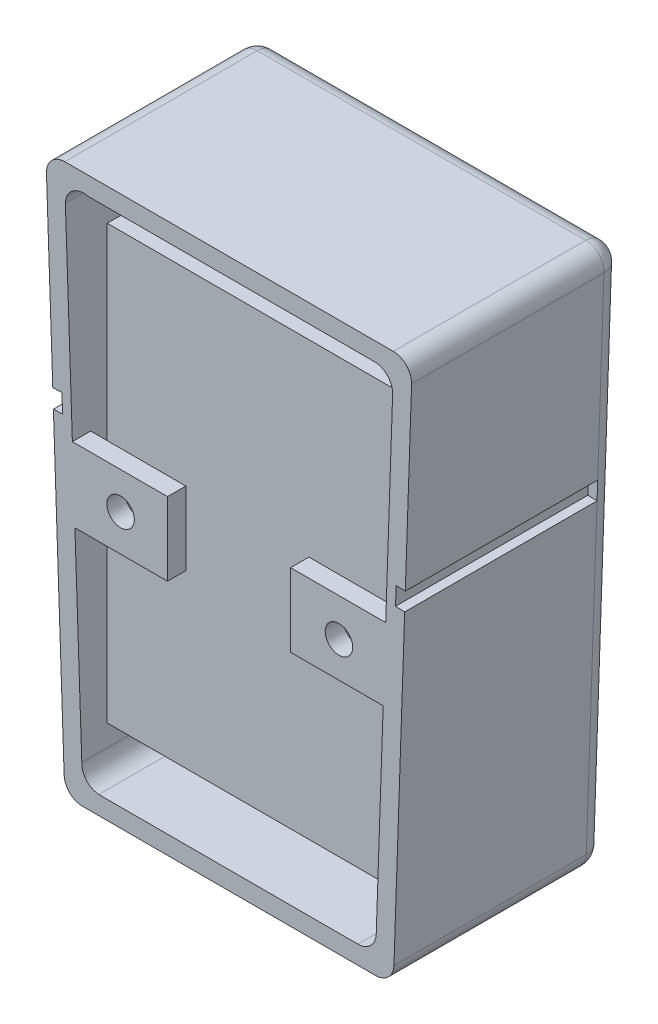
SolidWorks part; units mm, degrees
ref_plane "Front Plane" through (0, 0, 0) normal (0, 0, 1) x (1, 0, 0)
ref_plane "Top Plane" through (0, 0, 0) normal (0, 1, 0) x (1, 0, 0)
ref_plane "Right Plane" through (0, 0, 0) normal (1, 0, 0) x (0, 0, -1)
sketch "Sketch1" plane through (0, 0, 0) normal (0, 0, 1) x (1, 0, 0)
  line L8 (-22.7709, 76.1547) -> (22.7709, 76.1547)
  line L9 (25.3094, 73.5272) -> (22.8585, 2.4525)
  line L10 (20.32, 0) -> (-20.32, 0)
  line L11 (0, 76.1547) -> (0, 0) construction
  line L12 (-25.3094, 73.5272) -> (-22.8585, 2.4525)
  line L13 (-19.5413, 73.6147) -> (20.1418, 73.6147)
  line L14 (22.6803, 70.9872) -> (20.4046, 4.9925)
  line L15 (17.8661, 2.54) -> (-18.0612, 2.54)
  line L16 (-22.688, 71.2103) -> (-20.4122, 5.2126)
  arc A0 (22.8585, 2.4525) -> (20.32, 0) centre (20.32, 2.54) cw
  arc A1 (22.7709, 76.1547) -> (25.3094, 73.5272) centre (22.7709, 73.6147) cw
  arc A2 (-22.8585, 2.4525) -> (-20.32, 0) centre (-20.32, 2.54) ccw
  arc A3 (-22.7709, 76.1547) -> (-25.3094, 73.5272) centre (-22.7709, 73.6147) ccw
  circle A4 centre (0, 58.5396) radius 3.75
  circle A5 centre (0, 21.6223) radius 12.75
  arc A6 (20.4046, 4.9925) -> (17.8661, 2.54) centre (17.8661, 5.08) cw
  arc A7 (20.1418, 73.6147) -> (22.6803, 70.9872) centre (20.1418, 71.0747) cw
  arc A8 (-20.4122, 5.2126) -> (-18.0612, 2.54) centre (-17.876, 5.0732) ccw
  arc A9 (-19.5413, 73.6147) -> (-22.688, 71.2103) centre (-20.1487, 71.1484) ccw
  point P6 (22.7739, 0)
  point P9 (25.4, 76.1547)
  dimension "D2" = 76.2
  dimension "D3" = 2.54
  dimension "D5" = 7.5
  dimension "D6" = 24.7778
  dimension "D7" = 25.5
  dimension "D8" = 23.5056
  dimension "D12" = 2.54
  dimension "D13" = 2.54
  dimension "D15" = 2.54
  dimension "D1" = 25.4
  dimension "D4" = 40.64
  dimension "D9" = 65.9947
  dimension "D10" = 2.54
  dimension "D11" = 2.54
  dimension "D14" = 2.54
  dimension "D16" = 5.0732
  dimension "D17" = 5.2126
  dimension "D18" = 71.1484
  dimension "D19" = 71.2103
extrude "Boss-Extrude1" add sketch "Sketch1" along normal blind 3.81 contours L11 L13 A9 L16 A8 L15 A5 A4 | L13 L11 A4 A5 L15 A6 L14 A7 | L11 L8 A3 L12 A2 L10 L15 A8 L16 A9 L13 | L8 L11 L13 A7 L14 A6 L15 L10 A0 L9 A1
ref_plane "Plane1" through (0, 0, 3.81) normal (0, 0, 1) x (1, 0, 0)
sketch "Sketch4" plane through (0, 0, 3.81) normal (0, 0, 1) x (1, 0, 0)
  line L8 (-22.7709, 76.1547) -> (22.7709, 76.1547)
  line L9 (25.3094, 73.5272) -> (22.8585, 2.4525)
  line L10 (20.32, 0) -> (-20.32, 0)
  line L11 (0, 76.1547) -> (0, 0) construction
  line L12 (-25.3094, 73.5272) -> (-22.8585, 2.4525)
  line L13 (-19.5413, 73.6147) -> (20.1418, 73.6147)
  line L14 (22.6803, 70.9872) -> (20.4046, 4.9925)
  line L15 (17.8661, 2.54) -> (-18.0612, 2.54)
  line L16 (-22.688, 71.2103) -> (-20.4122, 5.2126)
  arc A0 (22.8585, 2.4525) -> (20.32, 0) centre (20.32, 2.54) cw
  arc A1 (22.7709, 76.1547) -> (25.3094, 73.5272) centre (22.7709, 73.6147) cw
  arc A2 (-22.8585, 2.4525) -> (-20.32, 0) centre (-20.32, 2.54) ccw
  arc A3 (-22.7709, 76.1547) -> (-25.3094, 73.5272) centre (-22.7709, 73.6147) ccw
  arc A6 (20.4046, 4.9925) -> (17.8661, 2.54) centre (17.8661, 5.08) cw
  arc A7 (20.1418, 73.6147) -> (22.6803, 70.9872) centre (20.1418, 71.0747) cw
  arc A8 (-20.4122, 5.2126) -> (-18.0612, 2.54) centre (-17.876, 5.0732) ccw
  arc A9 (-19.5413, 73.6147) -> (-22.688, 71.2103) centre (-20.1487, 71.1484) ccw
  point P6 (22.7739, 0)
  point P9 (25.4, 76.1547)
  dimension "D2" = 76.2
  dimension "D3" = 2.54
  dimension "D5" = 5.0732
  dimension "D6" = 5.2126
  dimension "D7" = 71.1484
  dimension "D8" = 71.2103
  dimension "D12" = 2.54
  dimension "D13" = 2.54
  dimension "D15" = 2.54
  dimension "D16" = 0
  dimension "D1" = 25.4
  dimension "D4" = 40.64
  dimension "D9" = 65.9947
  dimension "D10" = 2.54
  dimension "D11" = 2.54
  dimension "D14" = 2.54
extrude "Boss-Extrude3" add sketch "Sketch4" along normal blind 25.4
ref_plane "Plane2" through (0, 0, 13.335) normal (0, 0, 1) x (1, 0, 0)
sketch "Sketch7" plane through (0, 0, 13.335) normal (0, 0, 1) x (1, 0, 0)
  line L11 (0, 76.1547) -> (0, 0) construction
  line L13 (-19.5377, 73.6147) -> (20.1453, 73.6147)
  line L14 (22.6838, 70.9872) -> (20.4081, 4.9925)
  line L15 (17.8696, 2.54) -> (-18.0576, 2.54)
  line L16 (-22.6652, 71.1077) -> (-20.3894, 5.1099)
  line L17 (20.1418, 73.6147) -> (-19.5413, 73.6147) construction
  arc A6 (20.4081, 4.9925) -> (17.8696, 2.54) centre (17.8696, 5.08) cw
  arc A7 (20.1453, 73.6147) -> (22.6838, 70.9872) centre (20.1453, 71.0747) cw
  arc A8 (-20.3894, 5.1099) -> (-18.0576, 2.54) centre (-17.8497, 5.0715) ccw
  arc A9 (-19.5377, 73.6147) -> (-22.6652, 71.1077) centre (-20.1255, 71.1437) ccw
  point P6 (22.7739, 0)
  point P9 (25.4, 76.1547)
  dimension "D2" = 39.6831
  dimension "D3" = 65.9978
  dimension "D5" = 1.975
  dimension "D6" = 1.975
  dimension "D7" = 0
  dimension "D8" = 20.2239
  dimension "D12" = 2.54
  dimension "D13" = 2.54
  dimension "D15" = 2.54
  dimension "D11" = 20.1255
  dimension "D4" = 35.9272
  dimension "D9" = 65.9947
  dimension "D10" = 20.2012
extrude "Boss-Extrude4" add sketch "Sketch7" along normal blind 2.54
fillet "Fillet1" radius 2.54 8 edges at (0, 76.1547, 0) (-24.5976, 75.3796, 0) (-24.0839, 37.9898, 0) (-22.0848, 0.7133, 0) (0, 0, 0) (22.0848, 0.7133, 0) (24.0839, 37.9898, 0) (24.5976, 75.3796, 0)
sketch "Sketch8" plane through (0, 0, 29.21) normal (0, 0, 1) x (1, 0, 0)
  line L0 (-24.0839, 37.9898) -> (24.0839, 37.9898) construction
  line L1 (-25.3094, 73.5272) -> (-22.8585, 2.4525) construction
  line L2 (22.8585, 2.4525) -> (25.3094, 73.5272) construction
  line L3 (-21.3673, 32.9098) -> (-21.7176, 43.0698) construction
  line L4 (-22.688, 71.2103) -> (-20.4122, 5.2126) construction
  line L5 (-21.7176, 43.0698) -> (-8.5315, 43.0698)
  line L6 (-8.5315, 43.0698) -> (-8.5315, 32.9098)
  line L7 (-8.5315, 32.9098) -> (-21.3673, 32.9098)
  line L9 (0, 76.1547) -> (0, 0) construction
  line L10 (22.7709, 76.1547) -> (-22.7709, 76.1547) construction
  line L11 (-20.32, 0) -> (20.32, 0) construction
  line L12 (8.5315, 32.9098) -> (21.3673, 32.9098)
  line L13 (8.5315, 43.0698) -> (8.5315, 32.9098)
  line L14 (21.7176, 43.0698) -> (8.5315, 43.0698)
  line L15 (-21.3673, 32.9098) -> (-21.7176, 43.0698)
  line L16 (21.3673, 32.9098) -> (21.7176, 43.0698)
  dimension "D1" = 5.08
  dimension "D2" = 5.08
  dimension "D3" = 17.0629
extrude "Boss-Extrude6" add sketch "Sketch8" against normal blind 2.54
sketch "Sketch9" plane through (0, 0, 29.21) normal (0, 0, 1) x (1, 0, 0)
  line L0 (-15.1245, 43.0698) -> (-14.9494, 32.9098) construction
  line L1 (-8.5315, 43.0698) -> (-21.7176, 43.0698) construction
  line L2 (-21.3673, 32.9098) -> (-8.5315, 32.9098) construction
  line L3 (0.3003, 73.6147) -> (-0.0975, 2.54) construction
  line L4 (20.1418, 73.6147) -> (-19.5413, 73.6147) construction
  line L5 (-18.0612, 2.54) -> (17.8661, 2.54) construction
  circle A0 centre (-15.0369, 37.9898) radius 1.905
  circle A1 centre (15.2377, 37.8204) radius 1.905
  dimension "D1" = 3.81
extrude "Cut-Extrude1" cut sketch "Sketch9" against normal blind 2.54
sketch "Sketch10" plane through (0, 0, 0) normal (0, 0, -1) x (-1, 0, 0)
  line L0 (0, 73.6147) -> (0, 2.54) construction
  line L1 (22.7709, 73.6147) -> (-22.7709, 73.6147) construction
  line L2 (-20.32, 2.54) -> (20.32, 2.54) construction
  line L3 (-21.8533, 47.0045) -> (21.8533, 47.0045) construction
  line L4 (-22.7709, 73.6147) -> (-20.32, 2.54) construction
  line L5 (20.32, 2.54) -> (22.7709, 73.6147) construction
  line L6 (-21.8971, 48.2745) -> (21.8971, 48.2745)
  line L7 (21.8971, 48.2745) -> (21.8095, 45.7345)
  line L8 (21.8095, 45.7345) -> (-21.8095, 45.7345)
  line L9 (-21.8095, 45.7345) -> (-21.8971, 48.2745)
  dimension "D1" = 26.6102
  dimension "D2" = 1.27
  dimension "D3" = 1.27
extrude "Cut-Extrude2" cut sketch "Sketch10" against normal blind 1.27
sketch "Sketch11" plane through (-22.7469, -0.7844, 0) normal (-0.9994, -0.0345, 0) x (0, 0, 1)
  line L0 (2.54, 47.7456) -> (29.21, 47.7456) construction
  line L1 (2.54, 74.3558) -> (2.54, 3.2388) construction
  line L2 (29.21, 74.3558) -> (29.21, 3.2388) construction
  line L3 (29.21, 74.3558) -> (2.54, 74.3558) construction
  line L4 (2.54, 49.0156) -> (29.21, 49.0156)
  line L5 (29.21, 49.0156) -> (29.21, 46.4756)
  line L6 (29.21, 46.4756) -> (2.54, 46.4756)
  line L7 (2.54, 46.4756) -> (2.54, 49.0156)
  dimension "D1" = 26.6102
  dimension "D2" = 1.27
  dimension "D3" = 1.27
extrude "Cut-Extrude3" cut sketch "Sketch11" against normal blind 1.27
sketch "Sketch12" plane through (22.7469, -0.7844, 0) normal (0.9994, -0.0345, 0) x (0, 0, -1)
  line L0 (-29.21, 47.7456) -> (-2.54, 47.7456) construction
  line L1 (-29.21, 3.2388) -> (-29.21, 74.3558) construction
  line L2 (-2.54, 3.2388) -> (-2.54, 74.3558) construction
  line L3 (-29.21, 74.3558) -> (-2.54, 74.3558) construction
  line L4 (-2.54, 49.0156) -> (-29.21, 49.0156)
  line L5 (-29.21, 49.0156) -> (-29.21, 46.4756)
  line L6 (-29.21, 46.4756) -> (-2.54, 46.4756)
  line L7 (-2.54, 46.4756) -> (-2.54, 49.0156)
  dimension "D1" = 26.6102
  dimension "D2" = 1.27
  dimension "D3" = 1.27
extrude "Cut-Extrude4" cut sketch "Sketch12" against normal blind 1.27
sketch "Sketch13" plane through (0, 0, 15.875) normal (0, 0, 1) x (1, 0, 0)
  line L0 (0.3003, 73.6147) -> (0, 0) construction
  line L1 (-19.5413, 73.6147) -> (20.1418, 73.6147) construction
  line L2 (-20.066, 68.5347) -> (19.9136, 68.5347)
  line L3 (-20.066, 68.5347) -> (-20.066, 8.5399)
  line L4 (19.9136, 68.5347) -> (19.9136, 8.5399)
  line L5 (-20.066, 8.5399) -> (19.9136, 8.5399)
  line L6 (-20.32, 2.54) -> (-20.32, 65.1906) construction
  dimension "D1" = 39.9796
  dimension "D2" = 0.254
  dimension "D3" = 5.08
  dimension "D4" = 59.9948
extrude "Boss-Extrude7" add sketch "Sketch13" along normal blind 10.16
